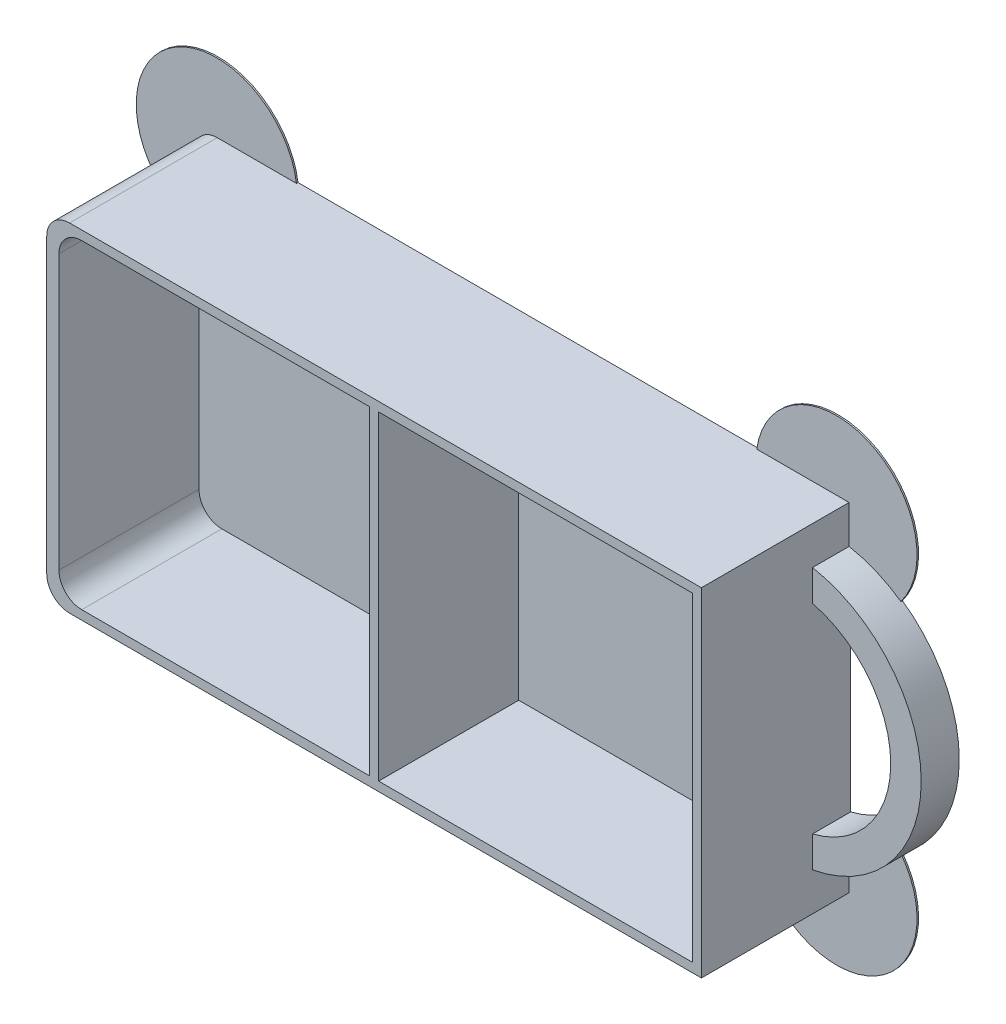
SolidWorks part; units mm, degrees
ref_plane "Спереди" through (0, 0, 0) normal (0, 0, 1) x (1, 0, 0)
ref_plane "Сверху" through (0, 0, 0) normal (0, 1, 0) x (1, 0, 0)
ref_plane "Справа" through (0, 0, 0) normal (1, 0, 0) x (0, 0, -1)
other "Configuration Table"
sketch "Эскиз1" plane through (0, 0, 0) normal (0, 0, 1) x (1, 0, 0)
  line L1 (-43, 22.2) -> (43, 22.2)
  line L2 (-43, 22.2) -> (-43, -22.2)
  line L3 (-43, -22.2) -> (43, -22.2)
  line L4 (43, 22.2) -> (43, -22.2)
  line L5 (-43, 22.2) -> (43, -22.2) construction
  line L6 (-43, -22.2) -> (43, 22.2) construction
  point P0 (0, 0)
  dimension "D1" = 86
  dimension "D2" = 44.4
extrude "Бобышка-Вытянуть1" add sketch "Эскиз1" along normal blind 19.6
sketch "Эскиз2" plane through (0, 0, 0) normal (0, 0, 1) x (1, 0, 0)
  line L0 (0, 0) -> (43, 0) construction
  line L1 (43, -22.2) -> (43, 22.2) construction
  line L2 (43, 17.2) -> (43, 13.1088)
  line L3 (43, -17.2) -> (43, -13.1088)
  arc A0 (43, -17.2) -> (43, 17.2) centre (39.7735, 0) ccw
  arc A1 (43, -13.1088) -> (43, 13.1088) centre (39.7735, 0) ccw
  dimension "D3" = 13.5
  dimension "D4" = 4
  dimension "D1" = 5
  dimension "D2" = 5
extrude "Бобышка-Вытянуть2" add sketch "Эскиз2" along normal blind 5
sketch "Эскиз3" plane through (0, 0, 19.6) normal (0, 0, 1) x (1, 0, 0)
  line L5 (-41.4, 22.2) -> (-41.4, -22.2)
  line L6 (-43, -21) -> (41.8, -21)
  line L7 (41.8, -21) -> (41.8, 21)
  line L8 (41.8, 21) -> (-43, 21)
  line L9 (-41.4, -21) -> (41.8, -21)
  line L10 (41.8, -21) -> (41.8, 21)
  line L11 (41.8, 21) -> (-41.4, 21)
  line L12 (-41.4, 21) -> (-41.4, -21)
  line L13 (-0.6, -21) -> (0.6, -21)
  line L14 (-0.6, -21) -> (-0.6, 21)
  line L15 (-0.6, 21) -> (0.6, 21)
  line L16 (0.6, -21) -> (0.6, 21)
  line L17 (-0.6, -21) -> (0.6, 21) construction
  line L18 (-0.6, 21) -> (0.6, -21) construction
  point P0 (0, 0)
  dimension "D3" = 1.2
  dimension "D4" = 40.8
  dimension "D5" = 41.2
  dimension "D6" = 42
  dimension "D1" = 1.2
  dimension "D2" = 1.6
extrude "Вырез-Вытянуть1" cut sketch "Эскиз3" against normal offset from surface (18.4 mm away) 1.2 contours L9 L14 L11 L12 | L16 L9 L10 L11 up to face at (48.1368, 0, 0)
fillet "Скругление1" radius 3 4 edges at (-43, 22.2, 9.8) (-43, -22.2, 9.8) (-41.4, -21, 10.4) (-41.4, 21, 10.4)
sketch "Эскиз4" plane through (0, 0, 0) normal (0, 0, -1) x (-1, 0, 0)
  line L0 (-43, 22.2) -> (40, 22.2) construction
  line L1 (43, 19.2) -> (43, -19.2) construction
  line L2 (-49.8115, 14.3349) -> (-30.8693, 22.2)
  line L3 (43, 10.5153) -> (29.589, 22.2)
  line L4 (50, 0) -> (-50, 0) construction
  line L5 (43, -10.5153) -> (29.589, -22.2)
  line L6 (-49.8115, -14.3349) -> (-30.8693, -22.2)
  arc A0 (-30.8693, 22.2) -> (-49.8115, 14.3349) centre (-41.3435, 20.6831) ccw
  arc A1 (-43, 17.2) -> (-43, -17.2) centre (-39.7735, 0) ccw construction
  arc A2 (29.589, 22.2) -> (43, 10.5153) centre (40.0631, 20.6831) cw
  arc A3 (29.589, -22.2) -> (43, -10.5153) centre (40.0631, -20.6831) ccw
  arc A4 (-30.8693, -22.2) -> (-49.8115, -14.3349) centre (-41.3435, -20.6831) cw
extrude "Бобышка-Вытянуть3" add sketch "Эскиз4" against normal blind 0.2
